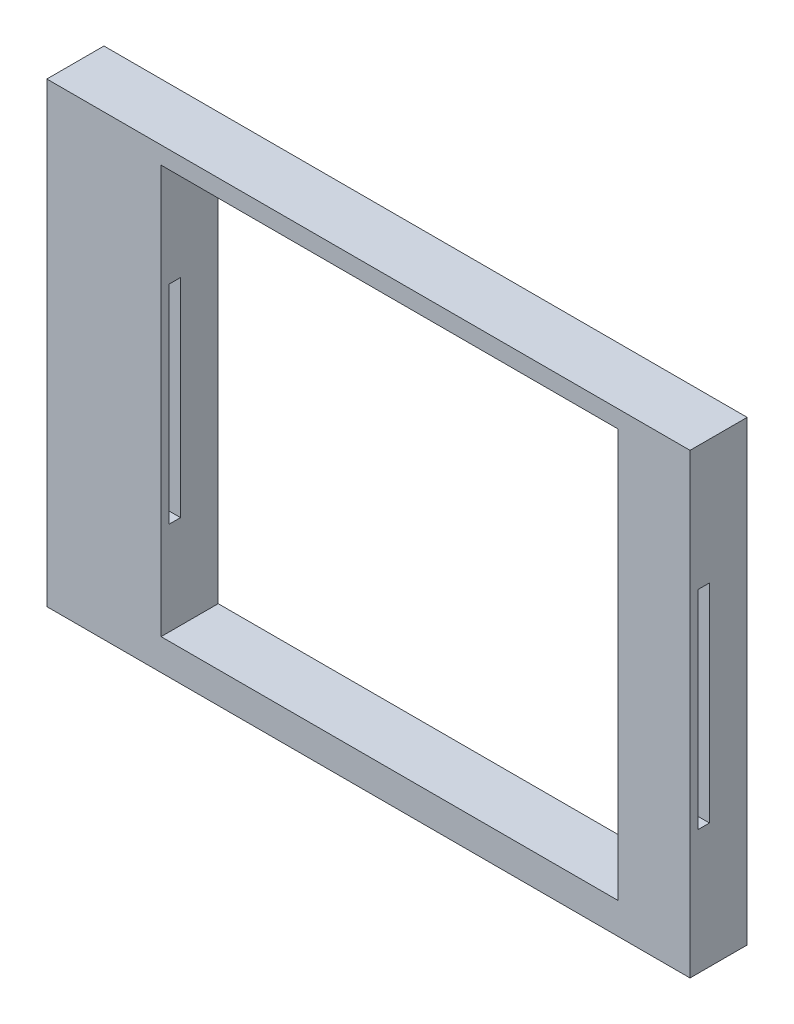
SolidWorks part; units mm, degrees
ref_plane "Front Plane" through (0, 0, 0) normal (0, 0, 1) x (1, 0, 0)
ref_plane "Top Plane" through (0, 0, 0) normal (0, 1, 0) x (1, 0, 0)
ref_plane "Right Plane" through (0, 0, 0) normal (1, 0, 0) x (0, 0, -1)
sketch "Sketch1" plane through (0, 0, 0) normal (0, 0, 1) x (1, 0, 0)
  line L1 (-26.8064, 48.2) -> (33.1936, 48.2)
  line L2 (-26.8064, 48.2) -> (-26.8064, 8.2)
  line L3 (-26.8064, 8.2) -> (33.1936, 8.2)
  line L4 (33.1936, 48.2) -> (33.1936, 8.2)
extrude "Boss-Extrude1" add sketch "Sketch1" along normal blind 5
sketch3d "3DSketch1"
  line L0 (-16.8064, 18.2, 5) -> (23.1936, 18.2, 5)
  line L1 (23.1936, 18.2, 5) -> (23.1936, 38.2, 5)
  line L2 (23.1936, 38.2, 5) -> (-16.8064, 38.2, 5)
  line L3 (-16.8064, 38.2, 5) -> (-16.8064, 18.2, 5)
  line L4 (-16.8064, 18.2, 5) -> (23.1936, 18.2, 5)
  line L5 (23.1936, 18.2, 5) -> (23.1936, 38.2, 5)
  line L6 (23.1936, 38.2, 5) -> (-16.8064, 38.2, 5)
  line L7 (-16.8064, 38.2, 5) -> (-16.8064, 18.2, 5)
  point P4 (0, 0, 0)
  point P5 (0, 0, 0)
  dimension "D1" = 10
extrude "Cut-Extrude2" cut sketch "3DSketch1" along direction (0, 0, 1) on the side of the normal through all both and the other way through all
sketch "Sketch2" plane through (-16.8064, 0, 0) normal (1, 0, 0) x (0, 0, -1)
  line L0 (-5, 38.2) -> (-5, 18.2) construction
  line L1 (-4.3, 37.3) -> (-3.3, 37.3)
  line L2 (-4.3, 37.3) -> (-4.3, 19.1)
  line L3 (-4.3, 19.1) -> (-3.3, 19.1)
  line L4 (-3.3, 37.3) -> (-3.3, 19.1)
  line L5 (-5, 18.2) -> (0, 18.2) construction
  line L6 (-5, 38.2) -> (0, 38.2) construction
  dimension "D1" = 1
  dimension "D2" = 0.7
  dimension "D3" = 0.9
  dimension "D4" = 0.9
extrude "Cut-Extrude3" cut sketch "Sketch2" against normal blind 7
sketch "Sketch3" plane through (23.1936, 0, 0) normal (-1, 0, 0) x (0, 0, 1)
  line L0 (5, 38.2) -> (0, 38.2) construction
  line L1 (3.3, 37.3) -> (4.3, 37.3)
  line L2 (3.3, 37.3) -> (3.3, 19.1)
  line L3 (3.3, 19.1) -> (4.3, 19.1)
  line L4 (4.3, 37.3) -> (4.3, 19.1)
  line L5 (5, 18.2) -> (0, 18.2) construction
  line L6 (5, 18.2) -> (5, 38.2) construction
  dimension "D1" = 0.9
  dimension "D2" = 0.9
  dimension "D3" = 0.7
  dimension "D4" = 1
extrude "Cut-Extrude4" cut sketch "Sketch3" against normal blind 7
sketch "Sketch6" plane through (0, 0, 5) normal (0, 0, 1) x (1, 0, 0)
  line L1 (-16.8064, 10.9264) -> (23.197, 10.9264)
  line L2 (-16.8064, 10.9264) -> (-16.8064, 46.6701)
  line L3 (-16.8064, 46.6701) -> (23.197, 46.6701)
  line L4 (23.197, 10.9264) -> (23.197, 46.6701)
extrude "Cut-Extrude5" cut sketch "Sketch6" against normal blind 7
sketch "Sketch7" plane through (0, 0, 5) normal (0, 0, 1) x (1, 0, 0)
  line L1 (29.4939, 52.3732) -> (41.576, 52.3732)
  line L2 (29.4939, 52.3732) -> (29.4939, 2.4387)
  line L3 (29.4939, 2.4387) -> (41.576, 2.4387)
  line L4 (41.576, 52.3732) -> (41.576, 2.4387)
extrude "Cut-Extrude6" cut sketch "Sketch7" against normal blind 7
